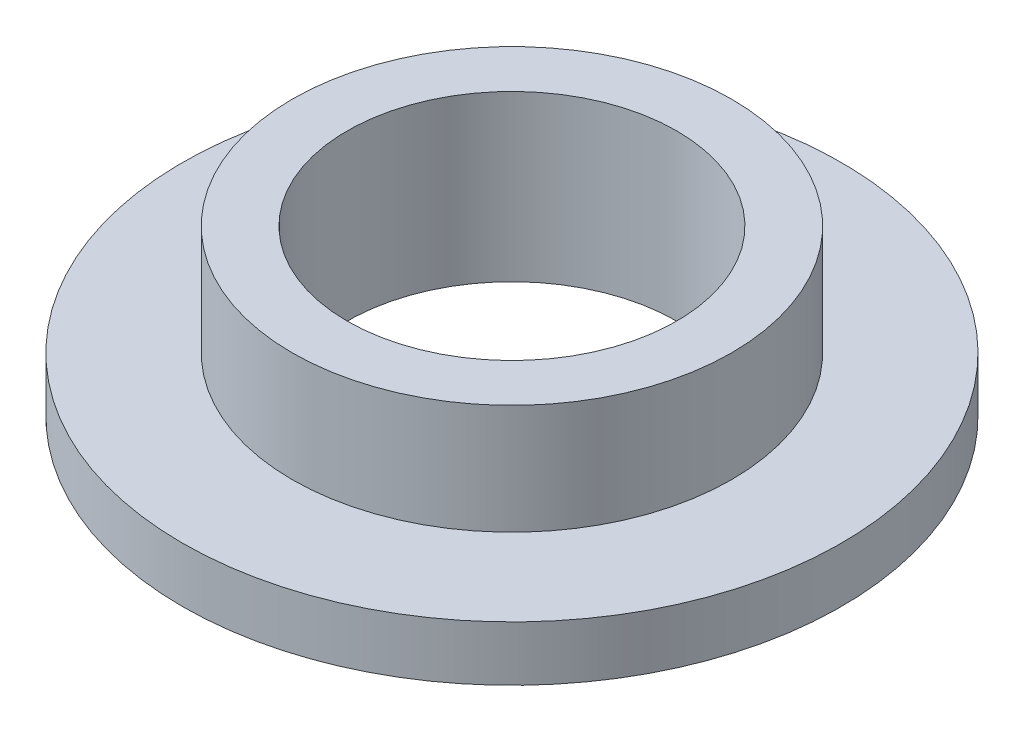
SolidWorks part; units mm, degrees
material "Brass"
ref_plane "Front Plane" through (0, 0, 0) normal (0, 0, 1) x (1, 0, 0)
ref_plane "Top Plane" through (0, 0, 0) normal (0, 1, 0) x (1, 0, 0)
ref_plane "Right Plane" through (0, 0, 0) normal (1, 0, 0) x (0, 0, -1)
sketch "Sketch2" plane through (0, 0, 0) normal (0, 1, 0) x (1, 0, 0)
  circle A0 centre (0, 0) radius 19.05
  dimension "D1" = 38.1
extrude "Boss-Extrude1" add sketch "Sketch2" along normal blind 3.175
sketch "Sketch3" plane through (0, 3.175, 0) normal (0, 1, 0) x (1, 0, 0)
  circle A0 centre (0, 0) radius 12.7
  dimension "D1" = 25.4
extrude "Boss-Extrude2" add sketch "Sketch3" along normal blind 6.35
sketch "Sketch4" plane through (0, 9.525, 0) normal (0, 1, 0) x (1, 0, 0)
  circle A0 centre (0, 0) radius 9.525
  dimension "D1" = 19.05
extrude "Cut-Extrude1" cut sketch "Sketch4" against normal through all
